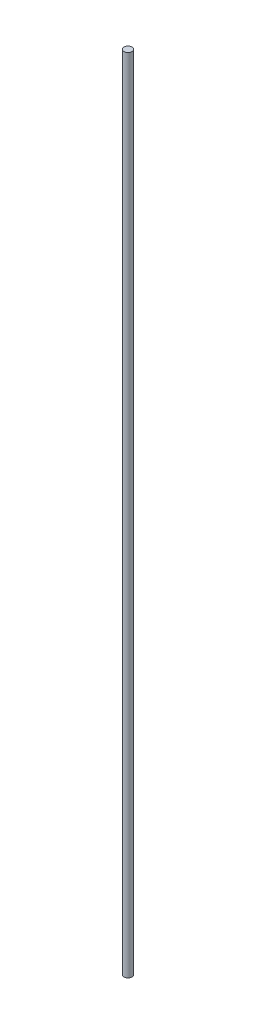
SolidWorks part; units mm, degrees
ref_plane "Front Plane" through (0, 0, 0) normal (0, 0, 1) x (1, 0, 0)
ref_plane "Top Plane" through (0, 0, 0) normal (0, 1, 0) x (1, 0, 0)
ref_plane "Right Plane" through (0, 0, 0) normal (1, 0, 0) x (0, 0, -1)
sketch "Sketch1" plane through (0, 0, 0) normal (0, 1, 0) x (1, 0, 0)
  circle A0 centre (-6.8772, 1.4386) radius 4
  dimension "D1" = 8
extrude "Boss-Extrude1" add sketch "Sketch1" along normal blind 800
